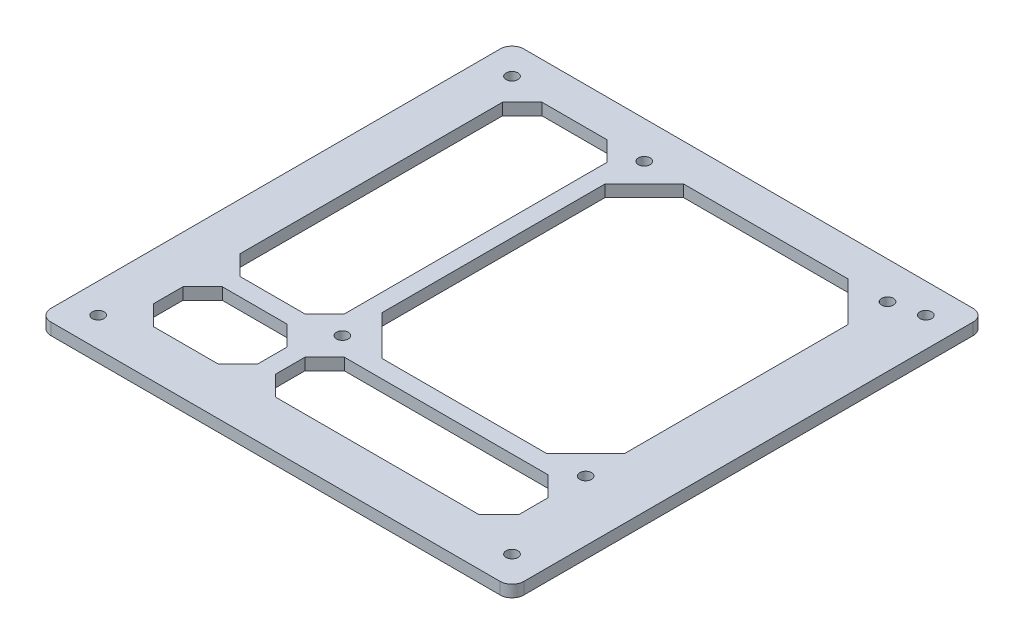
SolidWorks part; units mm, degrees
ref_plane "前基準面" through (0, 0, 0) normal (0, 0, 1) x (1, 0, 0)
ref_plane "上基準面" through (0, 0, 0) normal (0, 1, 0) x (1, 0, 0)
ref_plane "右基準面" through (0, 0, 0) normal (1, 0, 0) x (0, 0, -1)
ref_plane "平面1" through (0, 3, 0) normal (0, 1, 0) x (1, 0, 0)
sketch "草圖1" plane through (0, 3, 0) normal (0, 1, 0) x (1, 0, 0)
  line L0 (-60, 57) -> (-60, -57)
  line L1 (-57, -60) -> (57, -60)
  line L2 (60, -57) -> (60, 57)
  line L3 (57, 60) -> (-57, 60)
  line L4 (-48, -21) -> (-48, 45.6)
  line L5 (-48, 45.6) -> (-43, 50.6)
  line L6 (-43, 50.6) -> (-26.535, 50.6)
  line L7 (-26.535, 50.6) -> (-21.535, 45.6)
  line L8 (-21.535, 45.6) -> (-21.535, -21)
  line L9 (-21.535, -21) -> (-26.535, -26)
  line L10 (-26.535, -26) -> (-43, -26)
  line L11 (-43, -26) -> (-48, -21)
  line L12 (-17.035, -43) -> (-17.035, -35.5)
  line L13 (-17.035, -35.5) -> (-12.035, -30.5)
  line L14 (-12.035, -30.5) -> (39.685, -30.5)
  line L15 (39.685, -30.5) -> (44.685, -35.5)
  line L16 (44.685, -35.5) -> (44.685, -43)
  line L17 (44.685, -43) -> (39.685, -48)
  line L18 (39.685, -48) -> (-12.035, -48)
  line L19 (-12.035, -48) -> (-17.035, -43)
  line L20 (-48, -43) -> (-48, -35.5)
  line L21 (-48, -35.5) -> (-43, -30.5)
  line L22 (-43, -30.5) -> (-26.535, -30.5)
  line L23 (-26.535, -30.5) -> (-21.535, -35.5)
  line L24 (-21.535, -35.5) -> (-21.535, -43)
  line L25 (-21.535, -43) -> (-26.535, -48)
  line L26 (-26.535, -48) -> (-43, -48)
  line L27 (-43, -48) -> (-48, -43)
  line L28 (-7.035, 50.6) -> (34.685, 50.6)
  line L29 (34.685, 50.6) -> (44.685, 40.6)
  line L30 (44.685, 40.6) -> (44.685, -16)
  line L31 (44.685, -16) -> (34.685, -26)
  line L32 (34.685, -26) -> (-7.035, -26)
  line L33 (-7.035, -26) -> (-17.035, -16)
  line L34 (-17.035, -16) -> (-17.035, 40.6)
  line L35 (-17.035, 40.6) -> (-7.035, 50.6)
  arc A0 (-60, -57) -> (-57, -60) centre (-57, -57) ccw
  arc A1 (57, -60) -> (60, -57) centre (57, -57) ccw
  arc A2 (60, 57) -> (57, 60) centre (57, 57) ccw
  arc A3 (-57, 60) -> (-60, 57) centre (-57, 57) ccw
  circle A4 centre (-17.035, 50.6) radius 1.5
  circle A5 centre (44.685, 50.6) radius 1.5
  circle A6 centre (44.685, -26) radius 1.5
  circle A7 centre (-17.035, -26) radius 1.5
  circle A8 centre (52.5, -52.5) radius 1.5
  circle A9 centre (-52.5, 52.5) radius 1.5
  circle A10 centre (52.5, 52.5) radius 1.5
  circle A11 centre (-52.5, -52.5) radius 1.5
extrude "填料-伸長1" add sketch "草圖1" against normal blind 3
